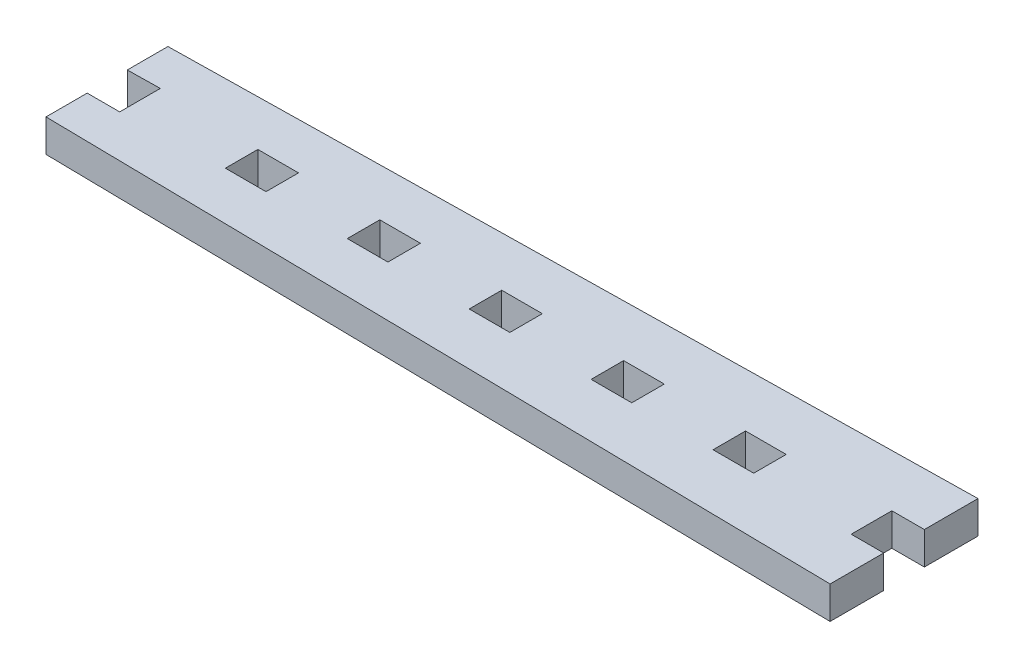
SolidWorks part; units mm, degrees
ref_plane "Front Plane" through (0, 0, 0) normal (0, 0, 1) x (1, 0, 0)
ref_plane "Top Plane" through (0, 0, 0) normal (0, 1, 0) x (1, 0, 0)
ref_plane "Right Plane" through (0, 0, 0) normal (1, 0, 0) x (0, 0, -1)
sketch "Sketch1" plane through (0, 0, 0) normal (0, 1, 0) x (1, 0, 0)
  line L0 (-0.4445, 12.618) -> (-0.4445, 18.9689)
  line L1 (-0.4452, -0.0811) -> (124.0148, -2.0276)
  line L2 (-0.4452, -0.0811) -> (-0.4452, 6.3544)
  line L3 (-0.4445, 18.9689) -> (124.0148, 21.0864)
  line L4 (124.0148, -2.0276) -> (124.0148, 6.3544)
  line L5 (-0.4445, 12.618) -> (4.6348, 12.7044)
  line L7 (-0.4452, 6.3544) -> (4.6348, 6.3544)
  line L8 (4.6348, 12.7044) -> (4.6348, 6.3544)
  line L9 (124.0148, 12.7044) -> (118.9348, 12.7044)
  line L11 (124.0148, 6.3544) -> (118.9348, 6.3544)
  line L12 (118.9348, 12.7044) -> (118.9348, 6.3544)
  line L13 (124.0148, 12.7044) -> (124.0148, 21.0864)
  point P13 (124.46, 19.05)
  point P14 (124.0553, 19.05)
  point P15 (0, 0)
  point P16 (123.7143, 21.1178)
  point P17 (4.6348, 9.5294)
  point P18 (118.9348, 9.5294)
  point P19 (124.0148, 24.0143)
  point P20 (0, 0)
  dimension "D1" = 19.05
  dimension "D2" = 124.46
  dimension "D3" = 6.35
  dimension "D4" = 6.35
  dimension "D5" = 5.08
  dimension "D6" = 23.114
extrude "Boss-Extrude1" add sketch "Sketch1" along normal blind 5.08
sketch "Sketch2" plane through (0, 5.08, 0) normal (0, 1, 0) x (1, 0, 0)
  line L0 (4.6348, 12.7044) -> (4.6348, 6.3544) construction
  line L1 (20.5098, 12.0694) -> (26.8598, 12.0694)
  line L2 (20.5098, 12.0694) -> (20.5098, 6.9894)
  line L3 (20.5098, 6.9894) -> (26.8598, 6.9894)
  line L4 (26.8598, 12.0694) -> (26.8598, 6.9894)
  point P6 (20.5098, 9.5294)
  point P9 (4.6348, 9.5294)
  dimension "D1" = 5.08
  dimension "D2" = 6.35
  dimension "D3" = 15.875
extrude "Cut-Extrude1" cut sketch "Sketch2" against normal through all
pattern_linear "LPattern1" count 5 spacing 19.05 along (1, 0, 0) of "Cut-Extrude1"
